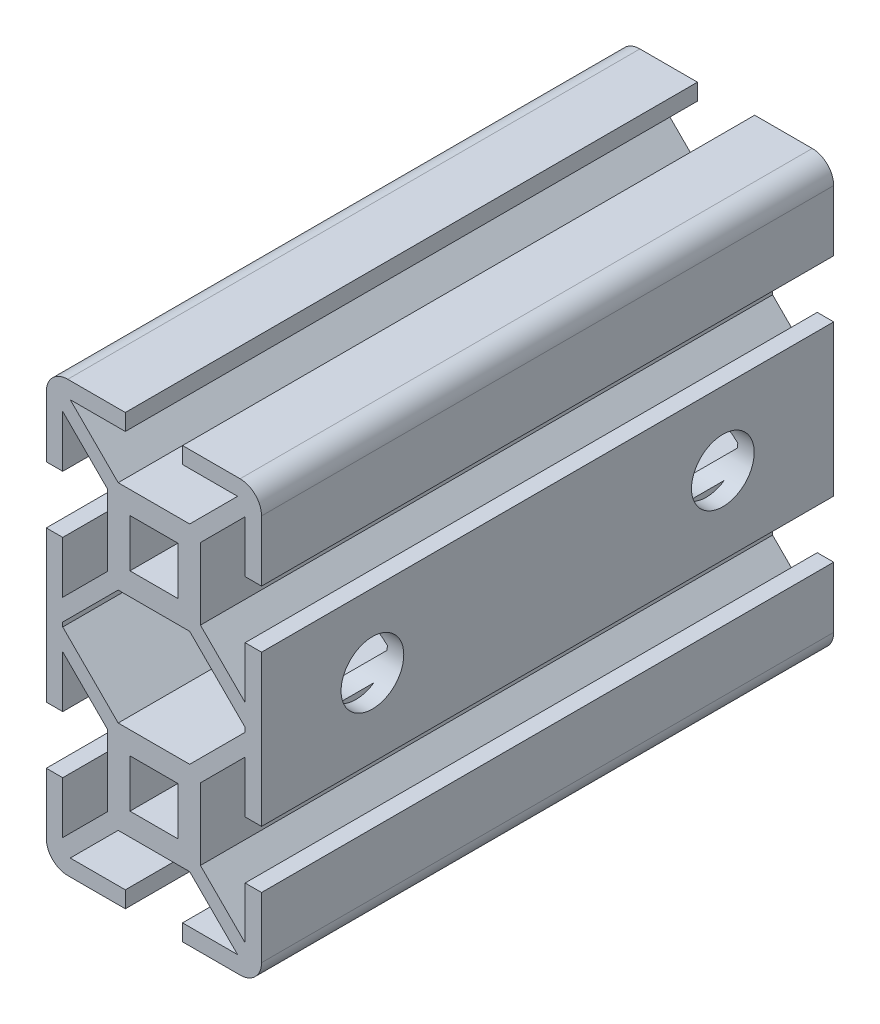
SolidWorks part; units mm, degrees
ref_plane "Alzado" through (0, 0, 0) normal (0, 0, 1) x (1, 0, 0)
ref_plane "Planta" through (0, 0, 0) normal (0, 1, 0) x (1, 0, 0)
ref_plane "Vista lateral" through (0, 0, 0) normal (1, 0, 0) x (0, 0, -1)
sketch "Croquis1" plane through (0, 0, 0) normal (0, 0, 1) x (1, 0, 0)
  line L0 (-15.05, 0) -> (15.05, 0) construction
  line L1 (-12.05, -30.05) -> (-4, -30.05)
  line L2 (-15.05, -27.05) -> (-15.05, -18.55)
  line L3 (-12.05, 30.05) -> (-4, 30.05)
  line L4 (15.05, -27.05) -> (15.05, -18.55)
  line L5 (-15.05, -30.05) -> (15.05, 30.05) construction
  line L6 (-15.05, 30.05) -> (15.05, -30.05) construction
  line L7 (-4, 30.05) -> (-4, 27.75)
  line L8 (-5, 8.05) -> (5, 8.05)
  line L9 (-6.5, 9.55) -> (-6.5, 19.55)
  line L10 (-5, 21.05) -> (5, 21.05)
  line L11 (6.5, 9.55) -> (6.5, 19.55)
  line L12 (-6.5, 8.05) -> (6.5, 21.05) construction
  line L13 (-6.5, 21.05) -> (6.5, 8.05) construction
  line L14 (15.05, 18.55) -> (15.05, 27.05)
  line L15 (-3.35, 11.2) -> (3.35, 11.2)
  line L16 (-3.35, 11.2) -> (-3.35, 17.9)
  line L17 (-3.35, 17.9) -> (3.35, 17.9)
  line L18 (3.35, 11.2) -> (3.35, 17.9)
  line L19 (-3.35, 11.2) -> (3.35, 17.9) construction
  line L20 (-3.35, 17.9) -> (3.35, 11.2) construction
  line L21 (-11.7, -27.75) -> (-4, -27.75)
  line L22 (-12.75, -25.8) -> (-12.75, -18.55)
  line L23 (-11.7, 27.75) -> (-4, 27.75)
  line L24 (12.75, -25.8) -> (12.75, -18.55)
  line L25 (-12.75, -27.75) -> (12.75, 27.75) construction
  line L26 (-12.75, 27.75) -> (12.75, -27.75) construction
  line L27 (4, 30.05) -> (4, 27.75)
  line L28 (12.75, 18.55) -> (12.75, 25.8)
  line L31 (-15.05, 18.55) -> (-12.75, 18.55)
  line L32 (-15.05, 10.55) -> (-12.75, 10.55)
  line L33 (15.05, 10.55) -> (12.75, 10.55)
  line L34 (15.05, 18.55) -> (12.75, 18.55)
  line L36 (-5, 21.05) -> (-11.7, 27.75)
  line L37 (-6.5, 21.05) -> (-12.75, 27.75) construction
  line L39 (-6.5, 19.55) -> (-12.75, 25.8)
  line L40 (6.5, 19.55) -> (12.75, 25.8)
  line L41 (5, 21.05) -> (11.7, 27.75)
  line L42 (6.5, -19.55) -> (12.75, -25.8)
  line L43 (5, -21.05) -> (11.7, -27.75)
  line L44 (-15.05, -30.05) -> (-4, -30.05)
  line L45 (-15.05, 30.05) -> (-4, 30.05)
  line L46 (-6.5, -19.55) -> (-12.75, -25.8)
  line L47 (-5, -21.05) -> (-11.7, -27.75)
  line L48 (4, -30.05) -> (4, -27.75)
  line L49 (-4, -30.05) -> (-4, -27.75)
  line L50 (-15.05, -10.55) -> (-12.75, -10.55)
  line L51 (-15.05, -18.55) -> (-12.75, -18.55)
  line L52 (15.05, -18.55) -> (12.75, -18.55)
  line L53 (15.05, -10.55) -> (12.75, -10.55)
  line L54 (-3.35, -11.2) -> (-3.35, -17.9)
  line L55 (-3.35, -17.9) -> (3.35, -17.9)
  line L56 (3.35, -11.2) -> (3.35, -17.9)
  line L57 (-3.35, -11.2) -> (3.35, -11.2)
  line L58 (-5, -8.05) -> (5, -8.05)
  line L59 (6.5, -9.55) -> (6.5, -19.55)
  line L60 (-6.5, -9.55) -> (-6.5, -19.55)
  line L61 (-5, -21.05) -> (5, -21.05)
  line L62 (4, -30.05) -> (12.05, -30.05)
  line L63 (6.5, -9.55) -> (12.75, -3.3)
  line L64 (5, -8.05) -> (11.7, -1.35)
  line L65 (-5, -8.05) -> (-11.7, -1.35)
  line L66 (-6.5, -9.55) -> (-12.75, -3.3)
  line L67 (-11.7, -1.35) -> (-12.75, -0.3)
  line L68 (11.7, -1.35) -> (12.75, -0.3)
  line L69 (-12.75, -0.3) -> (-12.75, 0.3)
  line L70 (12.75, -0.3) -> (12.75, 0.3)
  line L71 (6.5, 9.55) -> (12.75, 3.3)
  line L72 (5, 8.05) -> (11.7, 1.35)
  line L73 (-6.5, 9.55) -> (-12.75, 3.3)
  line L74 (-5, 8.05) -> (-11.7, 1.35)
  line L75 (-11.7, 1.35) -> (-12.75, 0.3)
  line L76 (11.7, 1.35) -> (12.75, 0.3)
  line L77 (-12.75, 3.3) -> (-12.75, 10.55)
  line L78 (12.75, 3.3) -> (12.75, 10.55)
  line L79 (15.05, -10.55) -> (15.05, 10.55)
  line L80 (12.75, -10.55) -> (12.75, -3.3)
  line L81 (-15.05, -10.55) -> (-15.05, 10.55)
  line L82 (-12.75, -10.55) -> (-12.75, -3.3)
  line L83 (4, -30.05) -> (15.05, -30.05)
  line L84 (4, -27.75) -> (11.7, -27.75)
  line L85 (4, 30.05) -> (12.05, 30.05)
  line L86 (4, 30.05) -> (15.05, 30.05)
  line L87 (4, 27.75) -> (11.7, 27.75)
  line L88 (-12.75, 18.55) -> (-12.75, 25.8)
  line L89 (-15.05, 18.55) -> (-15.05, 27.05)
  arc A0 (-12.05, -30.05) -> (-15.05, -27.05) centre (-12.05, -27.05) cw
  arc A1 (12.05, -30.05) -> (15.05, -27.05) centre (12.05, -27.05) ccw
  arc A2 (12.05, 30.05) -> (15.05, 27.05) centre (12.05, 27.05) cw
  arc A3 (-15.05, 27.05) -> (-12.05, 30.05) centre (-12.05, 27.05) cw
  point P0 (0, 0)
  point P8 (0, 14.55)
  point P9 (0, 14.55)
  point P20 (0, 0)
  point P55 (0, 11.2)
  point P72 (0, -11.2)
  dimension "D10" = 3
  dimension "D1" = 60.1
  dimension "D2" = 30.1
  dimension "D3" = 13
  dimension "D4" = 13
  dimension "D5" = 22
  dimension "D6" = 25.5
  dimension "D7" = 6.7
  dimension "D8" = 6.7
  dimension "D9" = 55.5
  dimension "D12" = 1.5
  dimension "D13" = 135
  dimension "D14" = 1.5
  dimension "D15" = 135
extrude "Saliente-Extruir1" add sketch "Croquis1" along normal blind 80 contours A3 L89 L31 L88 L39 L9 L73 L77 L32 L81 L50 L82 L66 L60 L46 L22 L51 L2 A0 L1 L49 L21 L47 L61 L43 L84 L48 L62 A1 L4 L52 L24 L42 L59 L63 L80 L53 L79 L33 L78 L71 L11 L40 L28 L34 L14 A2 L85 L27 L87 L41
sketch "Croquis2" plane through (15.05, 0, 0) normal (1, 0, 0) x (0, 0, -1)
  line L0 (-80, 0.3) -> (-64.5, 0.3) construction
  line L1 (-40, 27.05) -> (-40, -30.05) construction
  line L2 (-80, 27.05) -> (0, 27.05) construction
  line L3 (-80, -30.05) -> (0, -30.05) construction
  circle A0 centre (-64.5, 0.3) radius 4.384
  circle A1 centre (-15.5, 0.3) radius 4.384
  dimension "D1" = 15.5
extrude "Cortar-Extruir1" cut sketch "Croquis2" against normal blind 34
